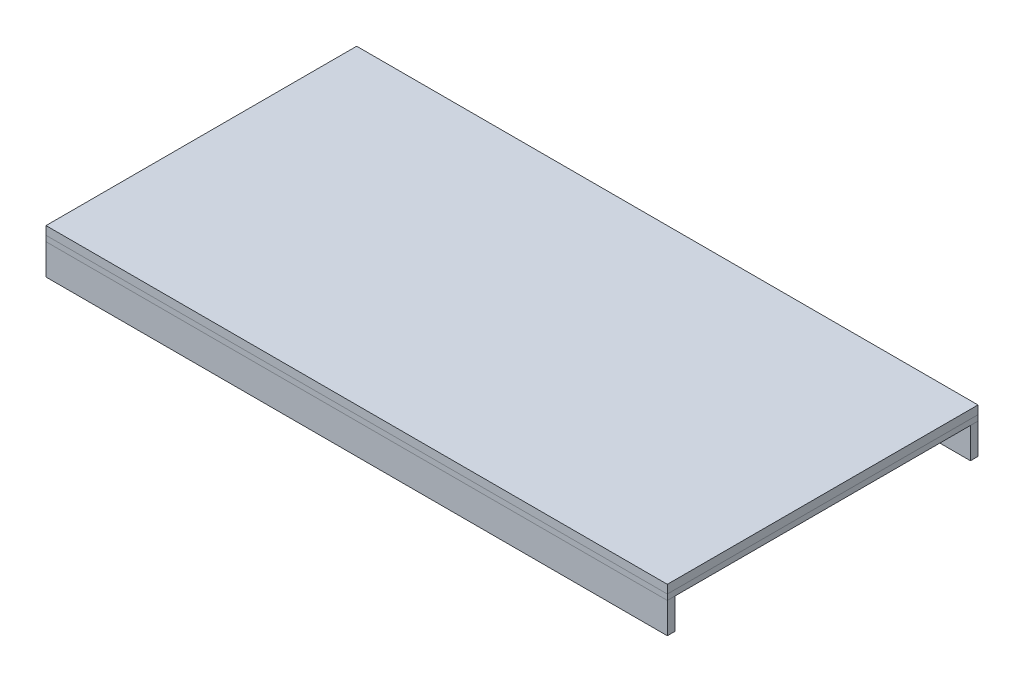
SolidWorks part; units mm, degrees
material "Pine"
ref_plane "Front Plane" through (0, 0, 0) normal (0, 0, 1) x (1, 0, 0)
ref_plane "Top Plane" through (0, 0, 0) normal (0, 1, 0) x (1, 0, 0)
ref_plane "Right Plane" through (0, 0, 0) normal (1, 0, 0) x (0, 0, -1)
sketch "Sketch1" plane through (0, 0, 0) normal (0, 1, 0) x (1, 0, 0)
  line L0 (0, -55) -> (0, 55) construction
  line L1 (-700, 350) -> (700, 350)
  line L2 (-700, 350) -> (-700, -350)
  line L3 (-700, -350) -> (700, -350)
  line L4 (700, 350) -> (700, -350)
  line L5 (-55, 0) -> (55, 0) construction
  dimension "D1" = 1400
  dimension "D2" = 700
  dimension "D3" = 700
  dimension "D4" = 350
extrude "Boss-Extrude1" add sketch "Sketch1" against normal blind 19
sketch "Sketch2" plane through (0, -19, 0) normal (0, -1, 0) x (1, 0, 0)
  line L4 (-700, 350) -> (-700, -350)
  line L5 (-700, -350) -> (700, -350)
  line L6 (700, -350) -> (700, 350)
  line L7 (700, 350) -> (-700, 350)
  line L8 (-700, 350) -> (-700, -350)
  line L9 (-700, -350) -> (700, -350)
  line L10 (700, -350) -> (700, 350)
  line L11 (700, 350) -> (-700, 350)
  dimension "D1" = 0
extrude "Boss-Extrude2" add sketch "Sketch2" along normal blind 12.5 separate body
sketch "Sketch3" plane through (700, 0, 0) normal (1, 0, 0) x (0, 0, -1)
  line L0 (350, -31.5) -> (-350, -31.5) construction
  line L1 (-350, -31.5) -> (-333, -31.5)
  line L2 (-350, -31.5) -> (-350, -100.5)
  line L3 (-350, -100.5) -> (-333, -100.5)
  line L4 (-333, -31.5) -> (-333, -100.5)
  line L5 (350, -31.5) -> (333, -31.5)
  line L6 (350, -31.5) -> (350, -100.5)
  line L7 (350, -100.5) -> (333, -100.5)
  line L8 (333, -31.5) -> (333, -100.5)
  dimension "D1" = 69
  dimension "D2" = 17
extrude "Boss-Extrude3" add sketch "Sketch3" against normal up to surface (1400 mm away) separate body up to face at (-700, -25.25, 0)
sketch "Sketch4" plane through (0, 0, -333) normal (0, 0, 1) x (1, 0, 0)
  line L2 (700, -31.5) -> (-700, -31.5) construction
  line L3 (-6.25, -31.5) -> (6.25, -31.5)
  line L4 (-6.25, -31.5) -> (-6.25, -100.5)
  line L7 (-6.25, -100.5) -> (6.25, -100.5)
  line L8 (6.25, -31.5) -> (6.25, -100.5)
  line L9 (-700, -100.5) -> (700, -100.5) construction
  line L10 (0, -55.275) -> (0, 55.275) construction
  line L11 (343.75, -31.5) -> (356.25, -31.5)
  line L12 (343.75, -31.5) -> (343.75, -100.5)
  line L13 (343.75, -100.5) -> (356.25, -100.5)
  line L14 (356.25, -31.5) -> (356.25, -100.5)
  line L15 (-343.75, -31.5) -> (-356.25, -31.5)
  line L16 (-343.75, -31.5) -> (-343.75, -100.5)
  line L17 (-343.75, -100.5) -> (-356.25, -100.5)
  line L18 (-356.25, -31.5) -> (-356.25, -100.5)
  dimension "D1" = 12.5
  dimension "D2" = 6.25
  dimension "D3" = 337.5
  dimension "D4" = 2
extrude "Boss-Extrude4" add sketch "Sketch4" along normal up to surface (666 mm away) separate body up to face at (0, -66, 333)
